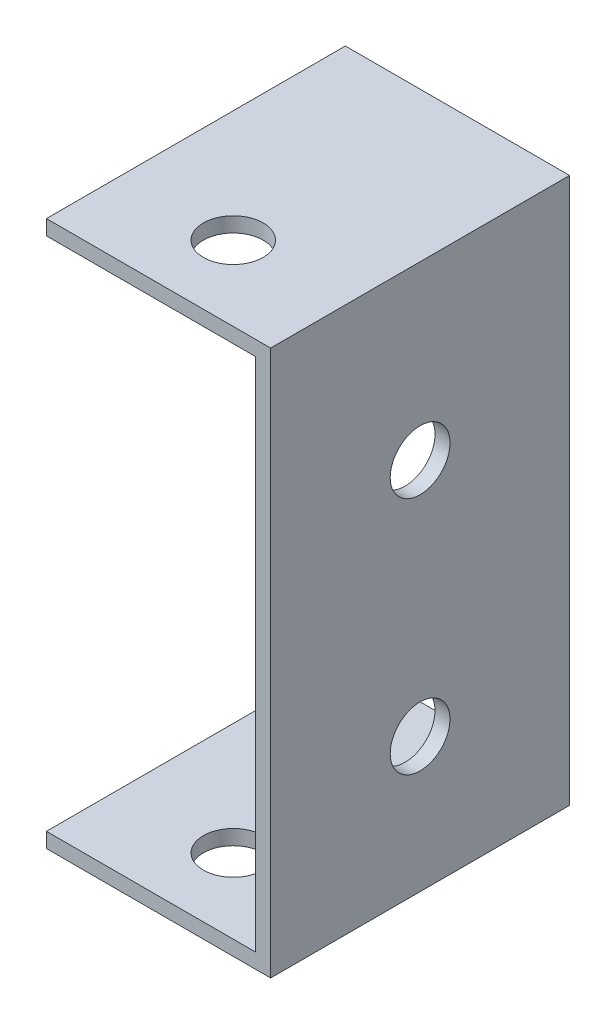
SolidWorks part; units mm, degrees
ref_plane "前视基准面" through (0, 0, 0) normal (0, 0, 1) x (1, 0, 0)
ref_plane "上视基准面" through (0, 0, 0) normal (0, 1, 0) x (1, 0, 0)
ref_plane "右视基准面" through (0, 0, 0) normal (1, 0, 0) x (0, 0, -1)
sketch "草图1" plane through (0, 0, 0) normal (0, 0, 1) x (1, 0, 0)
  line L0 (-61.1658, 46.995) -> (-31.1658, 46.995)
  line L1 (-31.1658, 46.995) -> (-31.1658, -26.005)
  line L2 (-31.1658, -26.005) -> (-61.1658, -26.005)
  line L3 (-61.1658, -26.005) -> (-61.1658, -24.005)
  line L4 (-61.1658, -24.005) -> (-33.1658, -24.005)
  line L5 (-33.1658, -24.005) -> (-33.1658, 44.995)
  line L6 (-33.1658, 44.995) -> (-61.1658, 44.995)
  line L7 (-61.1658, 44.995) -> (-61.1658, 46.995)
  dimension "D1" = 30
  dimension "D2" = 73
  dimension "D3" = 2
  dimension "D4" = 28
  dimension "D5" = 69
extrude "凸台-拉伸1" add sketch "草图1" along normal blind 40
sketch "草图3" plane through (-33.1658, 0, 0) normal (-1, 0, 0) x (0, 0, 1)
  line L0 (20, 44.995) -> (20, -24.005) construction
  line L1 (40, 44.995) -> (0, 44.995) construction
  line L2 (40, -24.005) -> (0, -24.005) construction
  line L3 (20, -24.005) -> (20, -8.005) construction
  line L4 (20, -8.005) -> (20, 23.995) construction
  circle A0 centre (20, 23.995) radius 4
  circle A1 centre (20, -8.005) radius 4
  dimension "D3" = 8
  dimension "D4" = 8
  dimension "D1" = 16
  dimension "D2" = 32
extrude "切除-拉伸1" cut sketch "草图3" against normal blind 40
sketch "草图4" plane through (0, 46.995, 0) normal (0, 1, 0) x (1, 0, 0)
  line L0 (-61.1658, -20) -> (-31.1658, -20) construction
  line L1 (-61.1658, -40) -> (-61.1658, 0) construction
  line L2 (-31.1658, -40) -> (-31.1658, 0) construction
  line L3 (-46.1658, -20) -> (-46.1658, -30) construction
  circle A1 centre (-46.1658, -30) radius 4
  dimension "D1" = 8
  dimension "D2" = 10
extrude "切除-拉伸2" cut sketch "草图4" against normal blind 96
